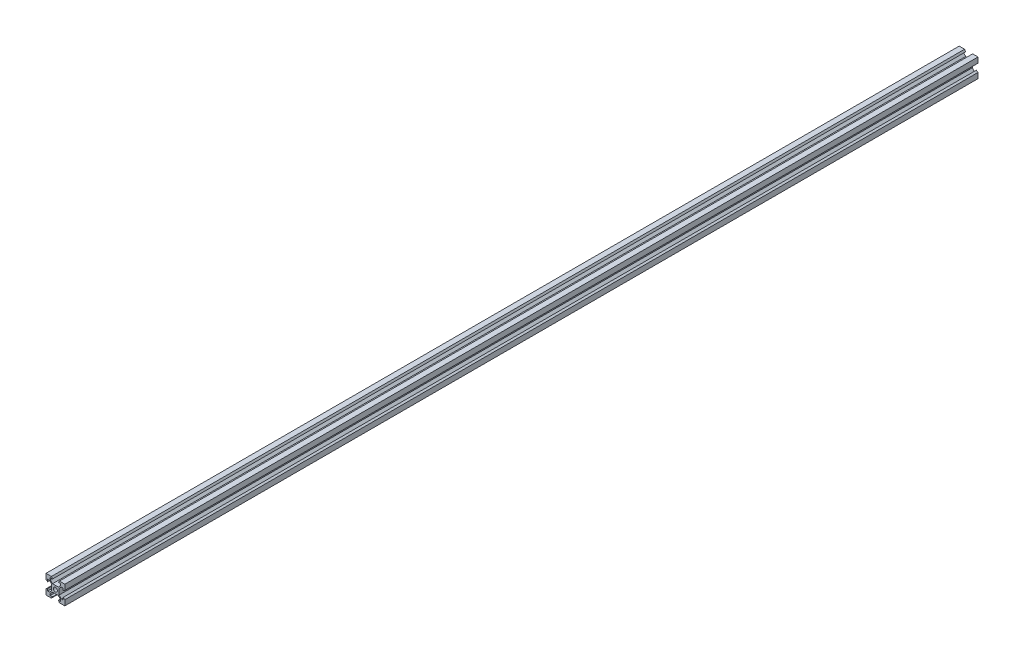
SolidWorks part; units mm, degrees
ref_plane "Front Plane" through (0, 0, 0) normal (0, 0, 1) x (1, 0, 0)
ref_plane "Top Plane" through (0, 0, 0) normal (0, 1, 0) x (1, 0, 0)
ref_plane "Right Plane" through (0, 0, 0) normal (1, 0, 0) x (0, 0, -1)
sketch "Sketch1" plane through (0, 0, 0) normal (0, 0, 1) x (1, 0, 0)
  line L0 (-10, 10) -> (-4.25, 10)
  line L1 (-4.25, 10) -> (-3.065, 8.2)
  line L2 (-3.065, 8.2) -> (-5.5, 8.2)
  line L3 (-5.5, 8.2) -> (-5.5, 6.3485)
  line L4 (-5.5, 6.3485) -> (-3.0515, 3.9)
  line L5 (-3.0515, 3.9) -> (0, 3.9)
  line L6 (-10, 10) -> (0, 0) construction
  line L7 (-3.9, 3.0515) -> (-3.9, 0)
  line L8 (-6.3485, 5.5) -> (-3.9, 3.0515)
  line L9 (-8.2, 3.065) -> (-8.2, 5.5)
  line L10 (-8.2, 5.5) -> (-6.3485, 5.5)
  line L11 (-10, 4.25) -> (-8.2, 3.065)
  line L12 (-10, 10) -> (-10, 4.25)
  line L13 (10, 10) -> (10, 4.25)
  line L14 (10, 10) -> (4.25, 10)
  line L15 (4.25, 10) -> (3.065, 8.2)
  line L16 (3.065, 8.2) -> (5.5, 8.2)
  line L17 (5.5, 8.2) -> (5.5, 6.3485)
  line L18 (8.2, 5.5) -> (6.3485, 5.5)
  line L19 (8.2, 3.065) -> (8.2, 5.5)
  line L20 (10, 4.25) -> (8.2, 3.065)
  line L21 (3.9, 3.0515) -> (3.9, 0)
  line L22 (6.3485, 5.5) -> (3.9, 3.0515)
  line L23 (5.5, 6.3485) -> (3.0515, 3.9)
  line L24 (3.0515, 3.9) -> (0, 3.9)
  line L25 (10, -10) -> (4.25, -10)
  line L26 (10, -10) -> (10, -4.25)
  line L27 (10, -4.25) -> (8.2, -3.065)
  line L28 (8.2, -3.065) -> (8.2, -5.5)
  line L29 (8.2, -5.5) -> (6.3485, -5.5)
  line L30 (5.5, -8.2) -> (5.5, -6.3485)
  line L31 (3.065, -8.2) -> (5.5, -8.2)
  line L32 (4.25, -10) -> (3.065, -8.2)
  line L33 (3.0515, -3.9) -> (0, -3.9)
  line L34 (5.5, -6.3485) -> (3.0515, -3.9)
  line L35 (6.3485, -5.5) -> (3.9, -3.0515)
  line L36 (3.9, -3.0515) -> (3.9, 0)
  line L37 (-10, -10) -> (-10, -4.25)
  line L38 (-10, -10) -> (-4.25, -10)
  line L39 (-4.25, -10) -> (-3.065, -8.2)
  line L40 (-3.065, -8.2) -> (-5.5, -8.2)
  line L41 (-5.5, -8.2) -> (-5.5, -6.3485)
  line L42 (-8.2, -5.5) -> (-6.3485, -5.5)
  line L43 (-8.2, -3.065) -> (-8.2, -5.5)
  line L44 (-10, -4.25) -> (-8.2, -3.065)
  line L45 (-3.9, -3.0515) -> (-3.9, 0)
  line L46 (-6.3485, -5.5) -> (-3.9, -3.0515)
  line L47 (-5.5, -6.3485) -> (-3.0515, -3.9)
  line L48 (-3.0515, -3.9) -> (0, -3.9)
  circle A0 centre (0, 0) radius 2.1
  point P58 (0, 0)
  dimension "D1" = 4.2
  dimension "D2" = 10
  dimension "D3" = 10
  dimension "D4" = 6.1
  dimension "D5" = 4.3
  dimension "D6" = 3.065
  dimension "D7" = 5.5
  dimension "D8" = 1.2
  dimension "D9" = 4.25
  dimension "D10" = 4
extrude "Boss-Extrude1" add sketch "Sketch1" along normal blind 970
